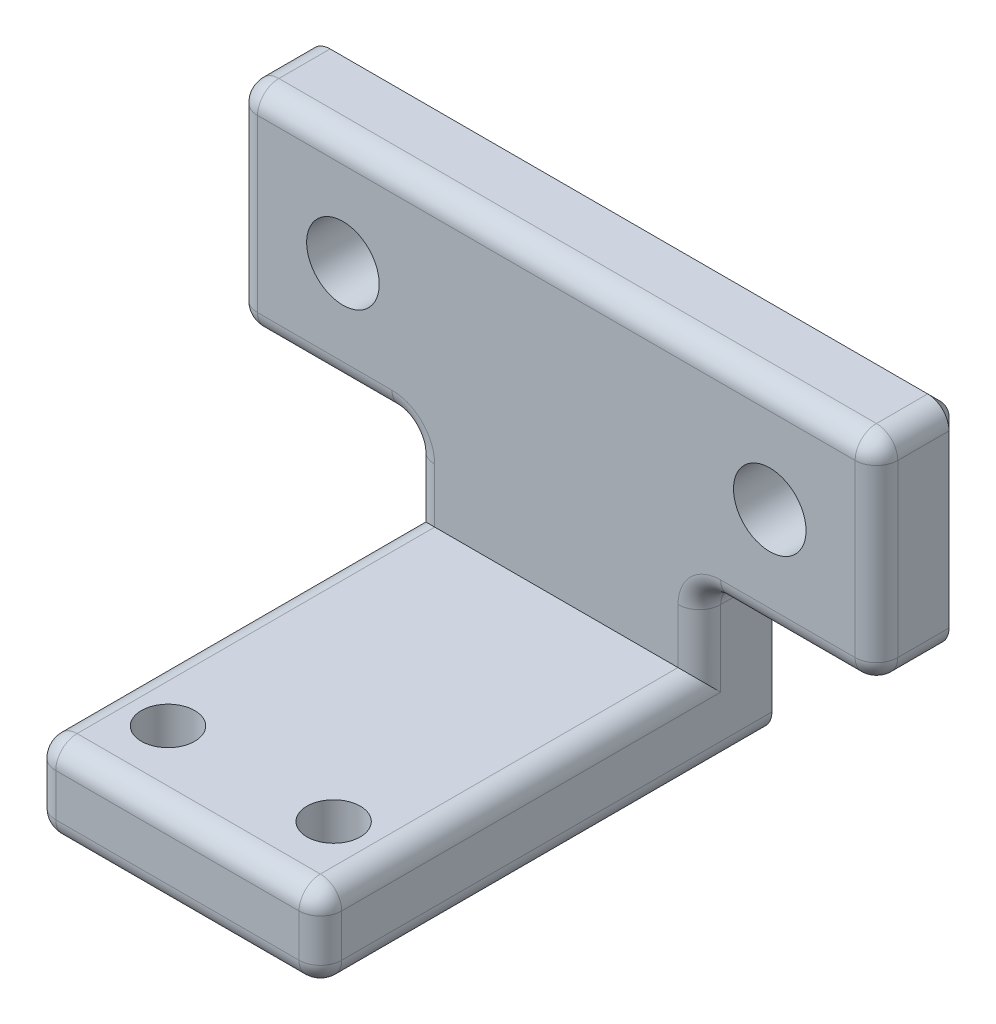
SolidWorks part; units mm, degrees
ref_plane "Front Plane" through (0, 0, 0) normal (0, 0, 1) x (1, 0, 0)
ref_plane "Top Plane" through (0, 0, 0) normal (0, 1, 0) x (1, 0, 0)
ref_plane "Right Plane" through (0, 0, 0) normal (1, 0, 0) x (0, 0, -1)
sketch "Sketch1" plane through (0, 0, 0) normal (0, 0, 1) x (1, 0, 0)
  line L0 (44.05, 0) -> (49.05, 0) construction
  line L1 (49.05, -5) -> (19.05, -5)
  line L2 (49.05, -5) -> (49.05, 5)
  line L3 (49.05, 5) -> (19.05, 5)
  line L4 (19.05, -5) -> (19.05, 5)
  line L5 (24.05, 0) -> (19.05, 0) construction
  line L6 (44.05, 0) -> (44.05, -5) construction
  line L7 (44.05, 0) -> (44.05, 5) construction
  line L8 (24.05, 0) -> (24.05, 5) construction
  line L9 (24.05, 0) -> (24.05, -5) construction
  circle A1 centre (44.05, 0) radius 1.7
  circle A2 centre (24.05, 0) radius 1.7
  dimension "D1" = 3.4
  dimension "D2" = 5
extrude "Boss-Extrude1" add sketch "Sketch1" along normal blind 4
sketch "Sketch2" plane through (27.35, 0, 0) normal (-1, 0, 0) x (0, 0, 1)
  line L0 (21.7564, -8.555) -> (4, -8.555)
  line L1 (4, -8.555) -> (4, -5)
  line L2 (21.7564, -8.555) -> (21.7564, -12.555)
  line L3 (21.7564, -12.555) -> (0, -12.555)
  line L4 (0, 13.5) -> (0, -13.5) construction
  line L5 (0, -12.555) -> (0, -5)
  line L6 (4, -5) -> (0, -5) construction
  line L7 (0, 5) -> (0, -5) construction
  line L8 (0, -5) -> (4, -5)
  dimension "D1" = 4
extrude "Boss-Extrude2" add sketch "Sketch2" against normal up to surface (410.407 mm away)
sketch "Sketch3" plane through (0, -8.555, 0) normal (0, 1, 0) x (1, 0, 0)
  circle A0 centre (30.17, -18.3164) radius 1.25
  circle A1 centre (37.93, -18.3164) radius 1.25
  dimension "D1" = 2.5
extrude "Cut-Extrude1" cut sketch "Sketch3" against normal blind 2
fillet "Fillet1" radius 1 21 edges at (44.9, -5, 4) (40.75, -6.7775, 4) (27.35, -6.7775, 4) (23.2, -5, 4) (19.05, 0, 4) (34.05, 5, 4) (49.05, 0, 4) (27.35, -10.555, 21.7564) (34.05, -12.555, 21.7564) (40.75, -10.555, 21.7564) (34.05, -8.555, 21.7564) (27.35, -8.555, 12.8782) (40.75, -8.555, 12.8782) (27.35, -12.555, 10.8782) (40.75, -12.555, 10.8782) (40.75, -5, 2) (49.05, -5, 2) (49.05, 5, 2) (19.05, 5, 2) (19.05, -5, 2) (27.35, -5, 2)
chamfer "Chamfer1" distance 0.6 angle 45 18 edges at (25.75, 0, 0) (45.75, 0, 0) (40.4571, -12.2621, 0) (40.75, -8.7775, 0) (41.0429, -5.2929, 0) (44.9, -5, 0) (48.7571, -4.7071, 0) (49.05, 0, 0) (48.7571, 4.7071, 0) (34.05, 5, 0) (19.3429, 4.7071, 0) (19.05, 0, 0) (19.3429, -4.7071, 0) (23.2, -5, 0) (27.0571, -5.2929, 0) (27.35, -8.7775, 0) (27.6429, -12.2621, 0) (34.05, -12.555, 0)
